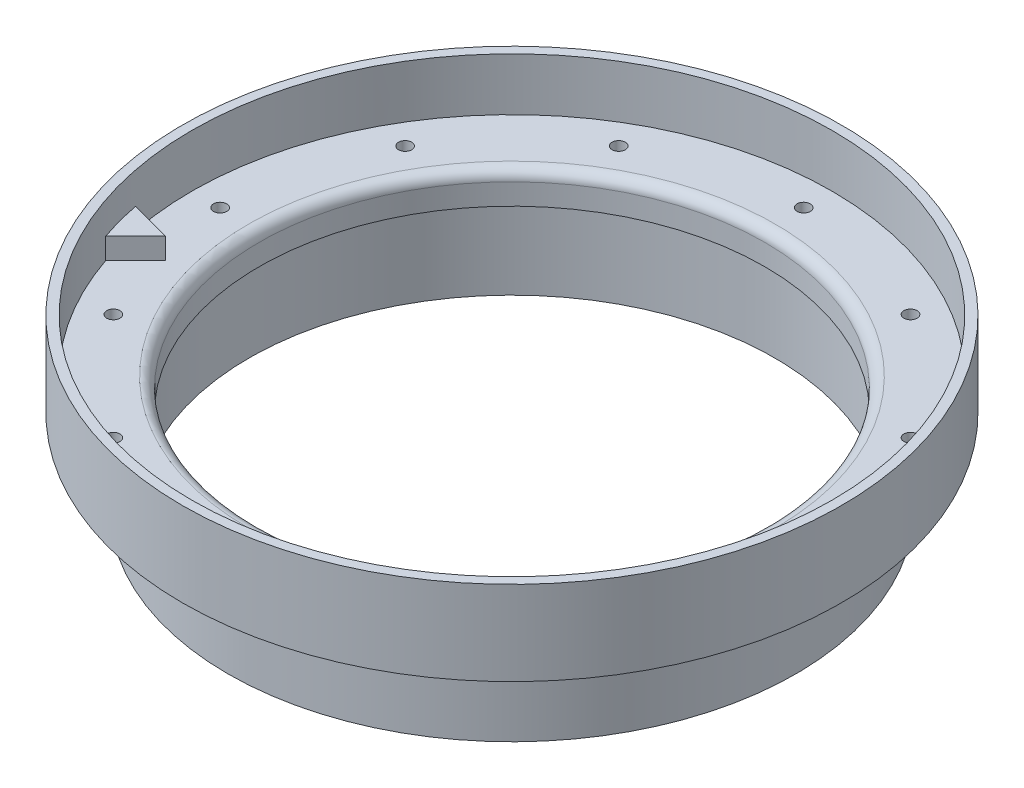
SolidWorks part; units mm, degrees
material "6061-T6 (SS)"
ref_plane "Front Plane" through (0, 0, 0) normal (0, 0, 1) x (1, 0, 0)
ref_plane "Top Plane" through (0, 0, 0) normal (0, 1, 0) x (1, 0, 0)
ref_plane "Right Plane" through (0, 0, 0) normal (1, 0, 0) x (0, 0, -1)
ref_axis "Axis1" through (0, 55, 0) along (0, -1, 0)
sketch "Cross Section" plane through (0, 0, 0) normal (0, 0, 1) x (1, 0, 0)
  line L0 (-38.1, 0) -> (-38.1, -3.175)
  line L1 (-38.1, -3.175) -> (-39.6367, -3.175)
  line L2 (-39.6367, -3.175) -> (-39.6367, -15.875)
  line L4 (0, -15.875) -> (-38.1, -15.875) construction
  line L5 (-42.8117, -15.875) -> (-42.8117, -3.175)
  line L6 (-42.8117, -3.175) -> (-49.6697, -3.175)
  line L7 (-49.6697, -3.175) -> (-49.6697, 9.525)
  line L8 (-49.6697, 9.525) -> (-48.26, 9.525)
  line L9 (-48.26, 9.525) -> (-48.26, 1.5875)
  line L11 (-38.1, 0) -> (0, 0) construction
  line L13 (-42.8117, -15.875) -> (-39.6367, -15.875)
  line L14 (-48.26, 1.5875) -> (-48.26, 3.175) construction
  line L15 (-39.6875, 1.5875) -> (-48.26, 1.5875)
  arc A0 (-39.6875, 1.5875) -> (-38.1, 0) centre (-39.6875, 0) cw
  dimension "D2" = 1.5875
  dimension "D1" = 1.5367
  dimension "D3" = 3.175
  dimension "D5" = 6.858
  dimension "D6" = 12.7
  dimension "D9" = 3.175
  dimension "D4" = 1.5875
  dimension "D7" = 38.1
revolve "Main" add sketch "Cross Section" angle 360 about axis through (0, 55, 0) along (0, -1, 0)
sketch "Hole Location" plane through (0, 0, 0) normal (0, 1, 0) x (1, 0, 0)
  line L0 (0, 0) -> (-43.9737, 0) construction
  circle A0 centre (0, 0) radius 43.9737 construction
  dimension "D1" = 87.9475
hole_wizard "#3-48 Tapped Hole1" positions "Sketch1" profile "Sketch2" tap size "#3-48" standard "ANSI Inch" end condition through all
sketch "Sketch1" plane through (0, 1.5875, 0) normal (0, 1, 0) x (1, 0, 0)
  point P0 (-43.9737, 0)
sketch "Sketch2" plane through (-43.9737, 1.5875, 0) normal (1, 0, 0) x (0, 0, 1)
  line L0 (0, 0) -> (0, 17.4625)
  line L1 (0, 17.4625) -> (0.9969, 17.4625)
  line L2 (0.9969, 17.4625) -> (0.9969, 0)
  line L5 (0.9969, 0) -> (0, 0)
  line L11 (0, -6.35) -> (0, 107.95) construction
  dimension "Thru Tap Drill Dia." = 1.9939
  dimension "Thru Tap Drill Depth" = 17.4625
cosmetic thread "Hole Thread1" parameters "D1"=4.7625, "D2"=2.5146
pattern_circular "CirPattern1" count 12 over 360 about axis through (0, 0, 0) along (0, 1, 0) of "#3-48 Tapped Hole1"
sketch "Sketch3" plane through (0, 1.5875, 0) normal (0, 1, 0) x (1, 0, 0)
  line L0 (0, 0) -> (-46.6156, -12.4906) construction
  line L1 (0, 0) -> (-43.9737, 0) construction
  line L2 (-45.6928, -15.5304) -> (-41.2027, -11.0402)
  line L3 (-41.2027, -11.0402) -> (-47.3363, -9.3967)
  circle A0 centre (0, 0) radius 48.26 construction
  circle A1 centre (0, 0) radius 48.26 construction
  arc A2 (-45.6928, -15.5304) -> (-47.3363, -9.3967) centre (0, 0) cw
  dimension "D1" = 15
  dimension "D2" = 60
  dimension "D3" = 6.35
extrude "Boss-Extrude1" add sketch "Sketch3" along normal blind 3.175
equation "\"D1@Hole Location\"=\"TANK DIAMETER@Cryo Tank.Assembly\"+\"GASKET SEAT THICKNESS@Cryo Tank.Assembly\"+\"LINER THICKNESS@Cryo Tank.Assembly\""
equation "\"D1@Cross Section\"=\"LINER THICKNESS@Cryo Tank.Assembly\"-0.002"
equation "\"D3@Cross Section\"=\"ALUMINUM LAP THICKNESS@Cryo Tank.Assembly\""
equation "\"D5@Cross Section\"=2*\"CF THICKNESS@Cryo Tank.Assembly\"+\"NOMEX THICKNESS@Cryo Tank.Assembly\""
equation "\"D7@Cross Section\"=\"TANK DIAMETER@Cryo Tank.Assembly\"/2"
